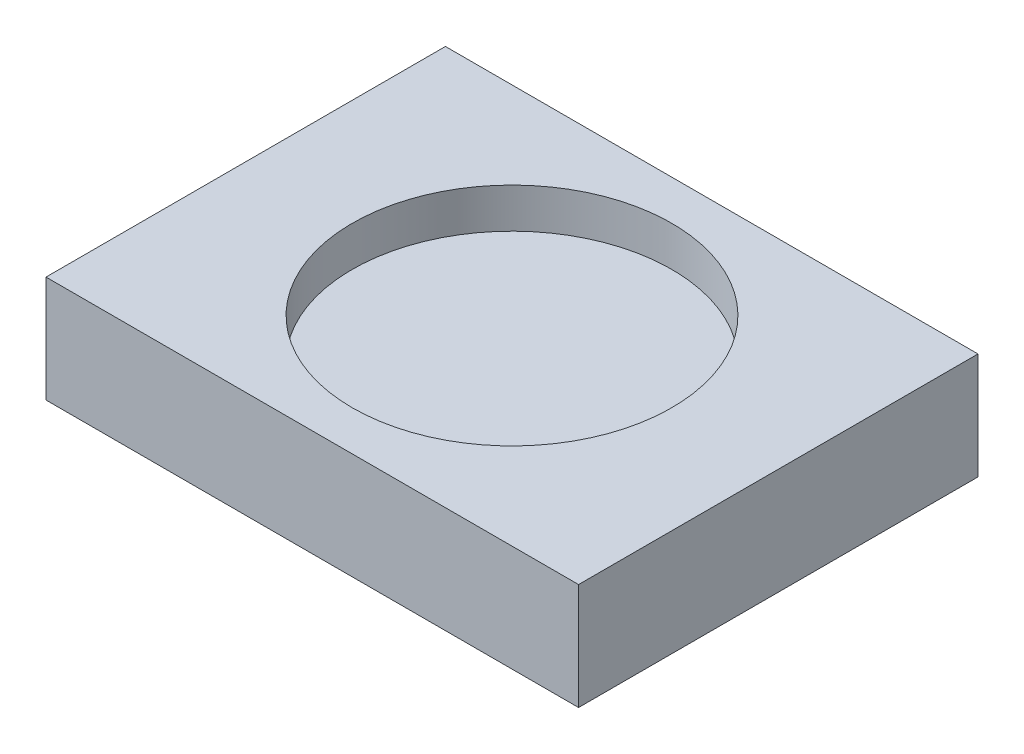
SolidWorks part; units mm, degrees
ref_plane "Front Plane" through (0, 0, 0) normal (0, 0, 1) x (1, 0, 0)
ref_plane "Top Plane" through (0, 0, 0) normal (0, 1, 0) x (1, 0, 0)
ref_plane "Right Plane" through (0, 0, 0) normal (1, 0, 0) x (0, 0, -1)
sketch "Sketch1" plane through (0, 0, 0) normal (0, 1, 0) x (1, 0, 0)
  line L1 (-100, 75) -> (100, 75)
  line L2 (-100, 75) -> (-100, -75)
  line L3 (-100, -75) -> (100, -75)
  line L4 (100, 75) -> (100, -75)
  line L5 (-100, 75) -> (100, -75) construction
  line L6 (-100, -75) -> (100, 75) construction
  point P0 (0, 0)
  dimension "D1" = 200
  dimension "D2" = 150
extrude "Boss-Extrude1" add sketch "Sketch1" along normal blind 40
sketch "Sketch2" plane through (0, 40, 0) normal (0, 1, 0) x (1, 0, 0)
  circle A0 centre (0, 0) radius 60
  dimension "D1" = 120
extrude "Cut-Extrude1" cut sketch "Sketch2" against normal blind 15
